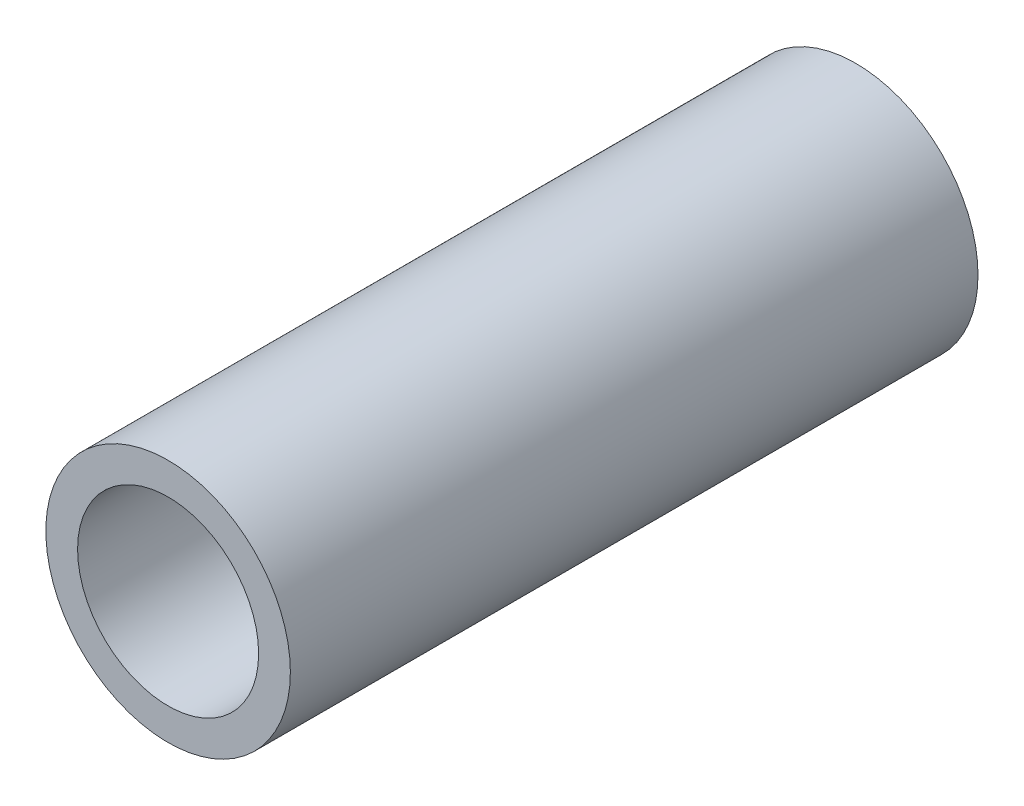
SolidWorks part; units mm, degrees
ref_plane "Front Plane" through (0, 0, 0) normal (0, 0, 1) x (1, 0, 0)
ref_plane "Top Plane" through (0, 0, 0) normal (0, 1, 0) x (1, 0, 0)
ref_plane "Right Plane" through (0, 0, 0) normal (1, 0, 0) x (0, 0, -1)
sketch "Sketch1" plane through (0, 0, 0) normal (0, 0, 1) x (1, 0, 0)
  circle A0 centre (0, 0) radius 10.668
  dimension "Pipe OD" = 21.336
extrude "Extrude-Thin1" add sketch "Sketch1" along normal mid plane 60 thin thin type one direction reverse wall 2.7686
